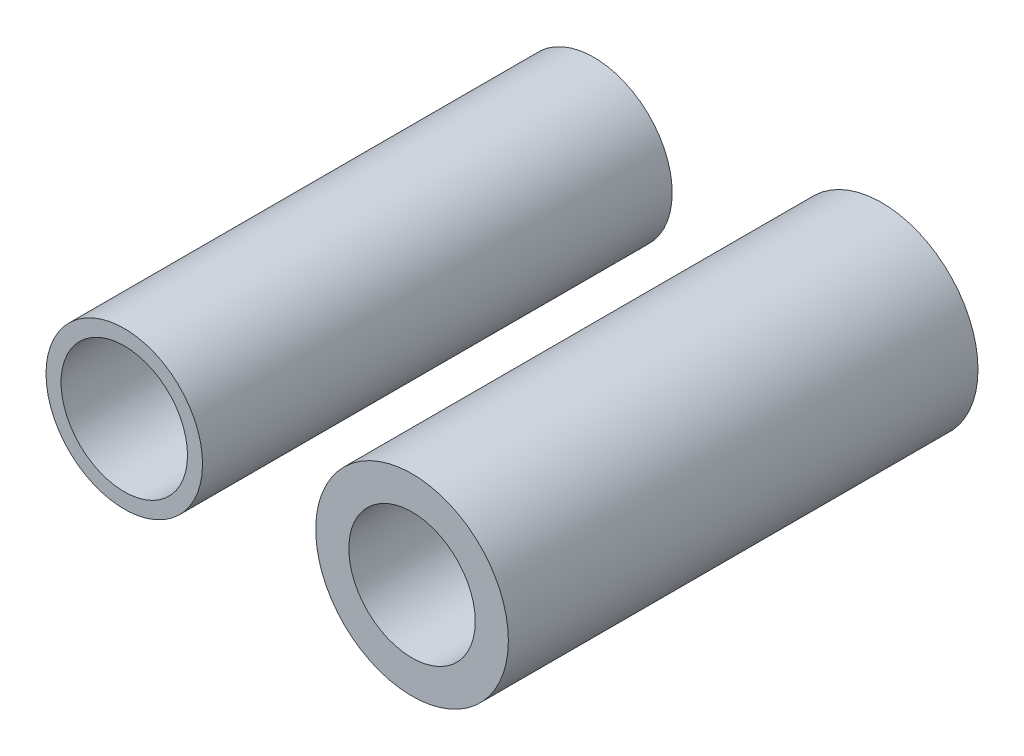
SolidWorks part; units mm, degrees
ref_plane "Front Plane" through (0, 0, 0) normal (0, 0, 1) x (1, 0, 0)
ref_plane "Top Plane" through (0, 0, 0) normal (0, 1, 0) x (1, 0, 0)
ref_plane "Right Plane" through (0, 0, 0) normal (1, 0, 0) x (0, 0, -1)
sketch "Sketch1" plane through (0, 0, 0) normal (0, 0, 1) x (1, 0, 0)
  circle A0 centre (0, 0) radius 4.064
extrude "Boss-Extrude1" add sketch "Sketch1" along normal blind 19.812 contours A0
sketch "Sketch2" plane through (0, 0, 0) normal (0, 0, -1) x (-1, 0, 0)
  circle A0 centre (12.1396, 0) radius 3.302
extrude "Boss-Extrude2" add sketch "Sketch2" against normal blind 19.812 separate body
sketch "Sketch3" plane through (0, 0, 19.812) normal (0, 0, 1) x (1, 0, 0)
  circle A0 centre (0, 0) radius 2.667
extrude "Cut-Extrude1" cut sketch "Sketch3" against normal blind 19.812
sketch "Sketch5" plane through (0, 0, 19.812) normal (0, 0, 1) x (1, 0, 0)
  circle A0 centre (-12.1396, 0) radius 2.667
extrude "Cut-Extrude2" cut sketch "Sketch5" against normal blind 19.812 contours A0
